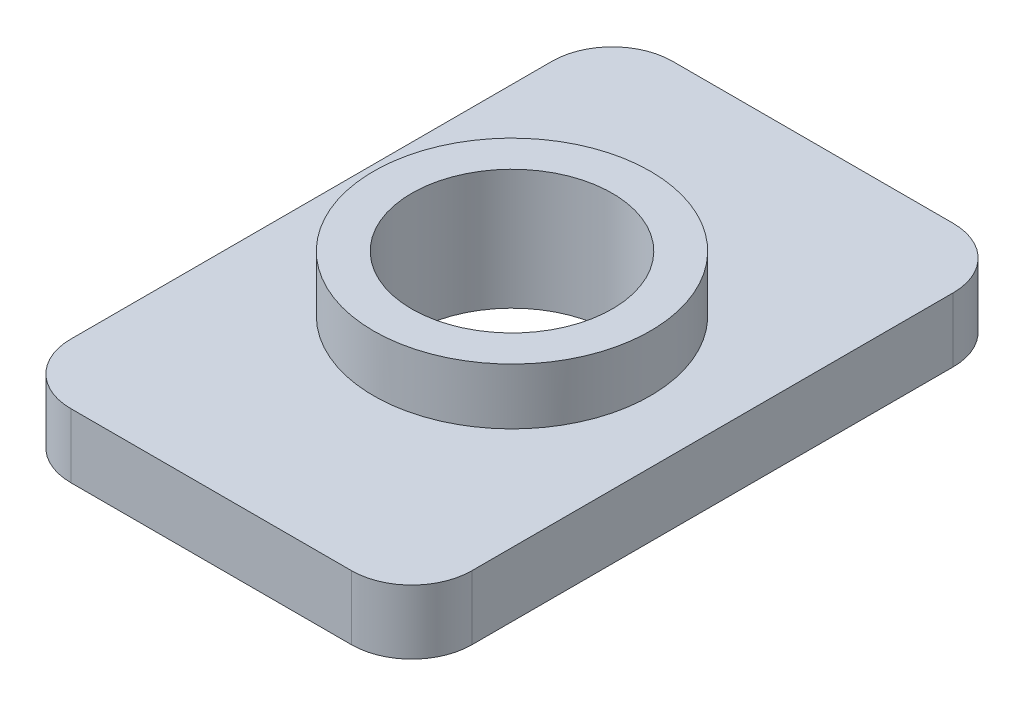
SolidWorks part; units mm, degrees
material "AISI 316 Stainless Steel Sheet (SS)"
ref_plane "Спереди" through (0, 0, 0) normal (0, 0, 1) x (1, 0, 0)
ref_plane "Сверху" through (0, 0, 0) normal (0, 1, 0) x (1, 0, 0)
ref_plane "Справа" through (0, 0, 0) normal (1, 0, 0) x (0, 0, -1)
sketch "Эскиз1" plane through (0, 0, 0) normal (0, 1, 0) x (1, 0, 0)
  line L1 (5, 7.5) -> (-5, 7.5)
  line L2 (5, 7.5) -> (5, -7.5)
  line L3 (5, -7.5) -> (-5, -7.5)
  line L4 (-5, 7.5) -> (-5, -7.5)
  line L5 (5, 7.5) -> (-5, -7.5) construction
  line L6 (5, -7.5) -> (-5, 7.5) construction
  circle A0 centre (0, 0) radius 2.5
  point P0 (0, 0)
  dimension "D3" = 5
  dimension "D1" = 10
  dimension "D2" = 15
extrude "Base" add sketch "Эскиз1" along normal blind 1.6
fillet "Fillet" radius 1.5 4 edges at (5, 0.8, -7.5) (-5, 0.8, -7.5) (-5, 0.8, 7.5) (5, 0.8, 7.5)
sketch "Эскиз2" plane through (0, 1.6, 0) normal (0, 1, 0) x (1, 0, 0)
  circle A0 centre (0, 0) radius 3.45
  circle A2 centre (0, 0) radius 2.5
  circle A3 centre (0, 0) radius 2.5 construction
  dimension "D1" = 6.9
extrude "ThreadBody" add sketch "Эскиз2" along normal blind 1.4
